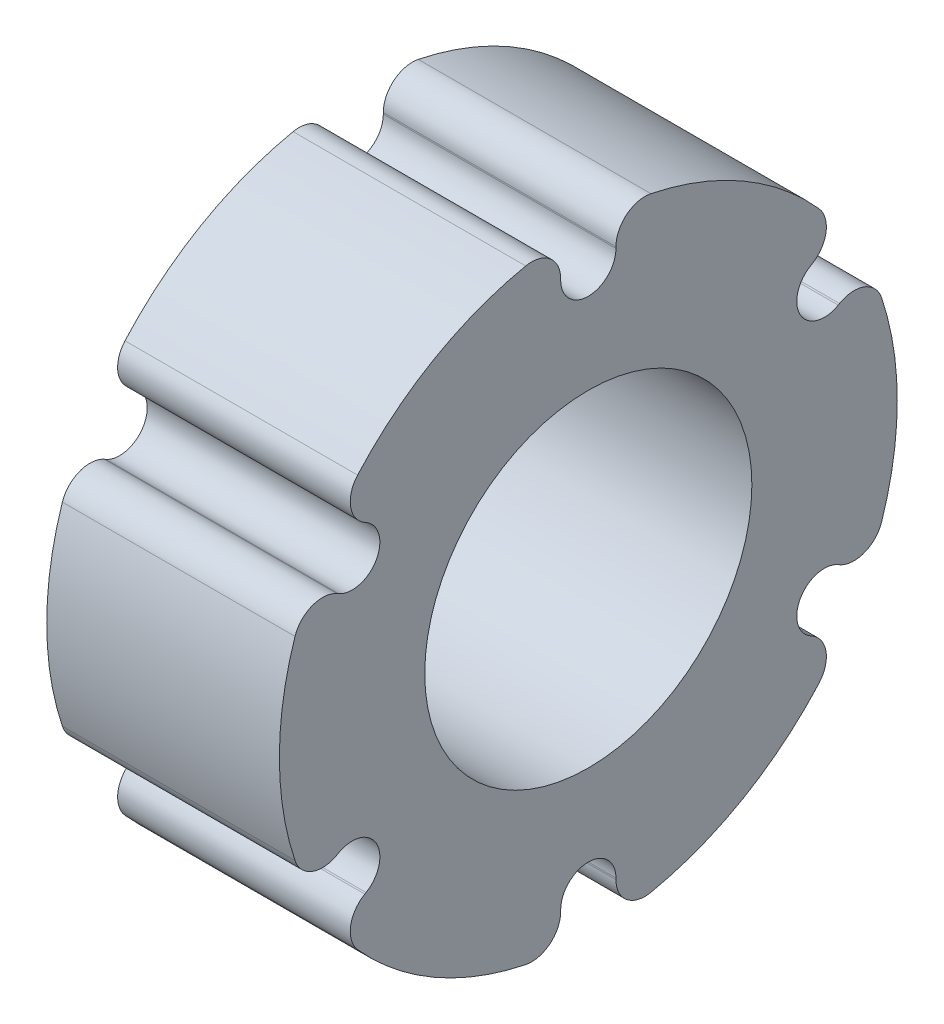
SolidWorks part; units mm, degrees
material "PET"
ref_plane "Front" through (0, 0, 0) normal (0, 0, 1) x (1, 0, 0)
ref_plane "Top" through (0, 0, 0) normal (0, 1, 0) x (1, 0, 0)
ref_plane "Right" through (0, 0, 0) normal (1, 0, 0) x (0, 0, -1)
sketch "Sketch1" plane through (0, 0, 0) normal (1, 0, 0) x (0, 0, -1)
  line L0 (-2.413, 23.8125) -> (-2.413, 23.9405)
  line L1 (2.413, 23.8125) -> (2.413, 23.9405)
  line L2 (19.4157, 13.996) -> (19.5266, 14.06)
  line L3 (21.8287, 9.8165) -> (21.9396, 9.8805)
  line L4 (21.8287, -9.8165) -> (21.9396, -9.8805)
  line L5 (19.4157, -13.996) -> (19.5266, -14.06)
  line L6 (2.413, -23.8125) -> (2.413, -23.9405)
  line L7 (-2.413, -23.8125) -> (-2.413, -23.9405)
  line L8 (-19.4157, -13.996) -> (-19.5266, -14.06)
  line L9 (-21.8287, -9.8165) -> (-21.9396, -9.8805)
  line L10 (-21.8287, 9.8165) -> (-21.9396, 9.8805)
  line L11 (-19.4157, 13.996) -> (-19.5266, 14.06)
  arc A0 (-5.4676, 26.4278) -> (-20.1534, 17.949) centre (0, 0) ccw
  circle A1 centre (0, 0) radius 23.8125 construction
  arc A2 (-2.413, 23.8125) -> (2.413, 23.8125) centre (0, 23.8125) ccw
  arc A3 (-2.413, 23.9405) -> (-5.4676, 26.4278) centre (-4.953, 23.9405) ccw
  arc A4 (2.413, 23.9405) -> (5.4676, 26.4278) centre (4.953, 23.9405) cw
  arc A5 (19.4157, 13.996) -> (21.8287, 9.8165) centre (20.6222, 11.9062) ccw
  arc A6 (19.5266, 14.06) -> (20.1534, 17.949) centre (18.2566, 16.2597) ccw
  arc A7 (21.9396, 9.8805) -> (25.621, 8.4788) centre (23.2096, 7.6808) cw
  arc A8 (21.8287, -9.8165) -> (19.4157, -13.996) centre (20.6222, -11.9063) ccw
  arc A9 (21.9396, -9.8805) -> (25.621, -8.4788) centre (23.2096, -7.6808) ccw
  arc A10 (19.5266, -14.06) -> (20.1534, -17.949) centre (18.2566, -16.2597) cw
  arc A11 (2.413, -23.8125) -> (-2.413, -23.8125) centre (0, -23.8125) ccw
  arc A12 (2.413, -23.9405) -> (5.4676, -26.4278) centre (4.953, -23.9405) ccw
  arc A13 (-2.413, -23.9405) -> (-5.4676, -26.4278) centre (-4.953, -23.9405) cw
  arc A14 (-19.4157, -13.996) -> (-21.8287, -9.8165) centre (-20.6222, -11.9062) ccw
  arc A15 (-19.5266, -14.06) -> (-20.1534, -17.949) centre (-18.2566, -16.2597) ccw
  arc A16 (-21.9396, -9.8805) -> (-25.621, -8.4788) centre (-23.2096, -7.6808) cw
  arc A17 (-21.8287, 9.8165) -> (-19.4157, 13.996) centre (-20.6222, 11.9063) ccw
  arc A18 (-21.9396, 9.8805) -> (-25.621, 8.4788) centre (-23.2096, 7.6808) ccw
  arc A19 (-19.5266, 14.06) -> (-20.1534, 17.949) centre (-18.2566, 16.2597) cw
  arc A20 (-25.621, 8.4788) -> (-25.621, -8.4788) centre (0, 0) ccw
  arc A21 (-20.1534, -17.949) -> (-5.4676, -26.4278) centre (0, 0) ccw
  arc A22 (20.1534, 17.949) -> (5.4676, 26.4278) centre (0, 0) ccw
  arc A23 (25.621, -8.4788) -> (25.621, 8.4788) centre (0, 0) ccw
  arc A24 (5.4676, -26.4278) -> (20.1534, -17.949) centre (0, 0) ccw
  circle A25 centre (0, 0) radius 14.2875
  point P59 (0, 0)
  dimension "D1" = 47.625
  dimension "D2" = 4.826
  dimension "D3" = 2.54
  dimension "D4" = 53.975
  dimension "D6" = 28.575
  dimension "D5" = 6
extrude "Boss-Extrude1" add sketch "Sketch1" along normal blind 20.32
